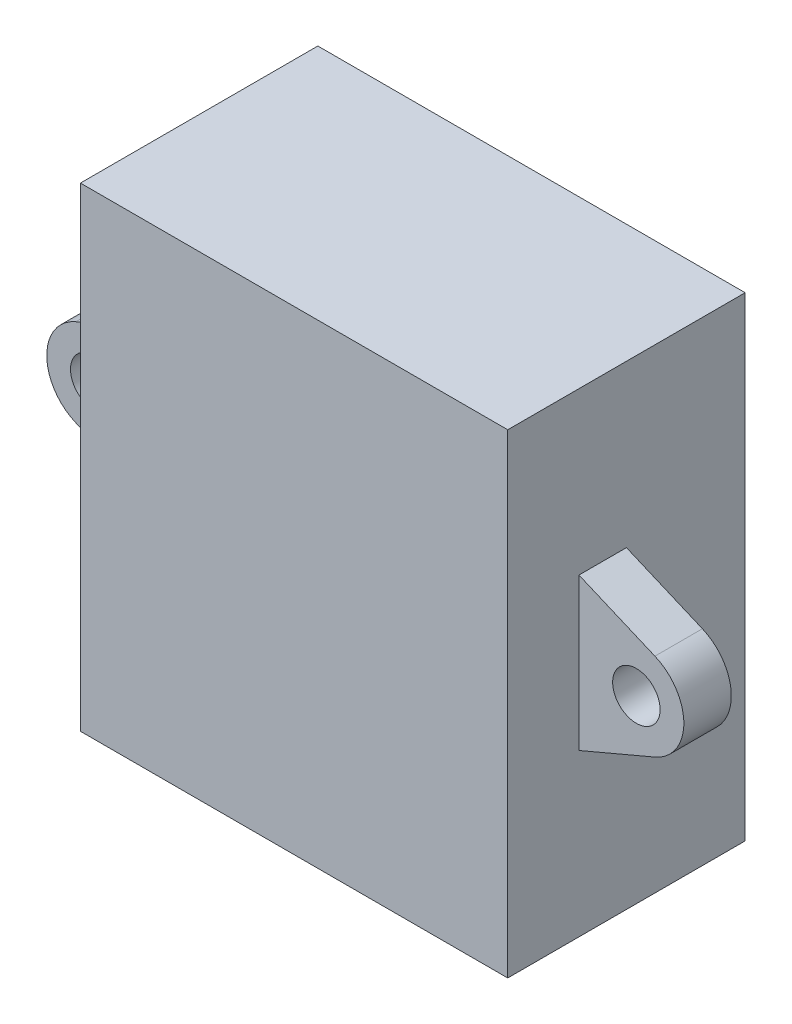
SolidWorks part; units mm, degrees
ref_plane "Front Plane" through (0, 0, 0) normal (0, 0, 1) x (1, 0, 0)
ref_plane "Top Plane" through (0, 0, 0) normal (0, 1, 0) x (1, 0, 0)
ref_plane "Right Plane" through (0, 0, 0) normal (1, 0, 0) x (0, 0, -1)
sketch "Sketch1" plane through (0, 0, 0) normal (0, 0, 1) x (1, 0, 0)
  line L1 (-57.4977, -5.8975) -> (-30.4977, -5.8975)
  line L2 (-57.4977, -5.8975) -> (-57.4977, -35.8975)
  line L3 (-57.4977, -35.8975) -> (-30.4977, -35.8975)
  line L4 (-30.4977, -5.8975) -> (-30.4977, -35.8975)
  dimension "D2" = 27
  dimension "D8" = 30
extrude "Boss-Extrude3" add sketch "Sketch1" along normal blind 15 contours L4 L1 L2 L3
ref_plane "Plane1" through (0, 0, 7.5) normal (0, 0, 1) x (1, 0, 0)
sketch "Sketch5" plane through (0, 0, 7.5) normal (0, 0, 1) x (1, 0, 0)
  line L0 (-30.4977, -16.0975) -> (-25.6977, -18.1362)
  line L3 (-25.6977, -23.6587) -> (-30.4977, -25.6975)
  line L4 (-30.4977, -16.0975) -> (-30.4977, -25.6975)
  line L5 (-57.4977, -16.0975) -> (-57.4977, -25.6975)
  line L7 (-62.2977, -23.6587) -> (-57.4977, -25.6975)
  line L8 (-57.4977, -16.0975) -> (-62.2977, -18.1362)
  arc A0 (-25.6977, -23.6587) -> (-25.6977, -18.1362) centre (-26.8705, -20.8975) ccw
  circle A1 centre (-26.8705, -20.8975) radius 1.5
  circle A4 centre (-61.1249, -20.8975) radius 1.5
  arc A5 (-62.2977, -23.6587) -> (-62.2977, -18.1362) centre (-61.1249, -20.8975) cw
  dimension "D1" = 3
  dimension "D4" = 9.6
  dimension "D9" = 3
  dimension "D10" = 3
  dimension "D11" = 3
  dimension "D2" = 4.8
  dimension "D3" = 4.8
  dimension "D7" = 9.6
  dimension "D8" = 4.8
  dimension "D12" = 4.8
  dimension "D13" = 27
extrude "Boss-Extrude7" add sketch "Sketch5" along normal blind 3
